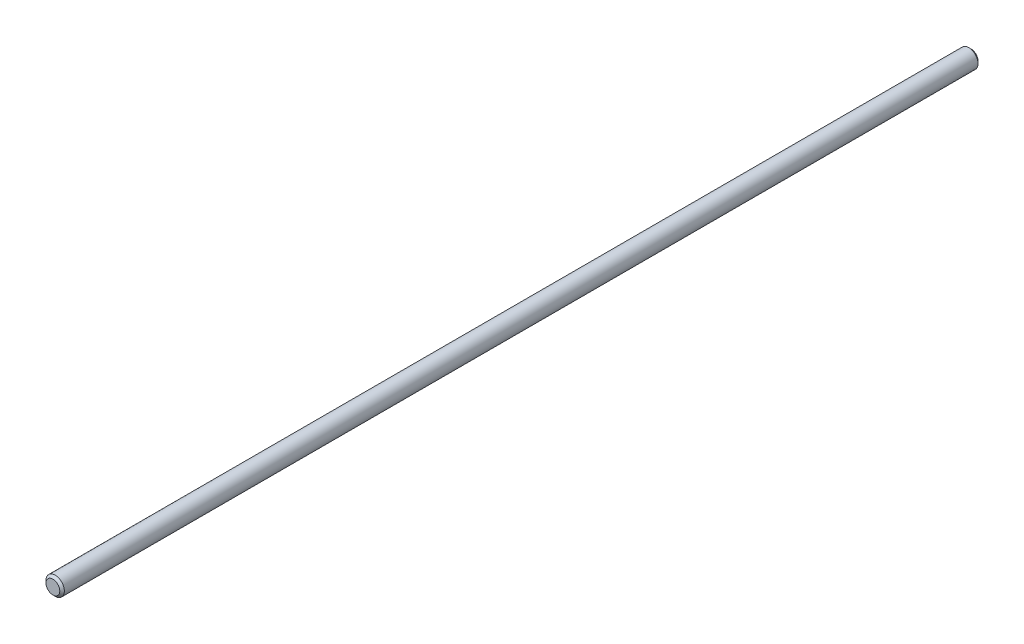
SolidWorks part; units mm, degrees
ref_plane "Piano frontale" through (0, 0, 0) normal (0, 0, 1) x (1, 0, 0)
ref_plane "Piano superiore" through (0, 0, 0) normal (0, 1, 0) x (1, 0, 0)
ref_plane "Piano destro" through (0, 0, 0) normal (1, 0, 0) x (0, 0, -1)
sketch "Schizzo1" plane through (0, 0, 0) normal (0, 0, 1) x (1, 0, 0)
  circle A0 centre (0, 0) radius 4
  dimension "D1" = 8
extrude "Estrusione-Estrusione1" add sketch "Schizzo1" along normal blind 400
chamfer "Smusso1" distance 1 angle 45 2 edges at (4, 0, 400) (4, 0, 0)
